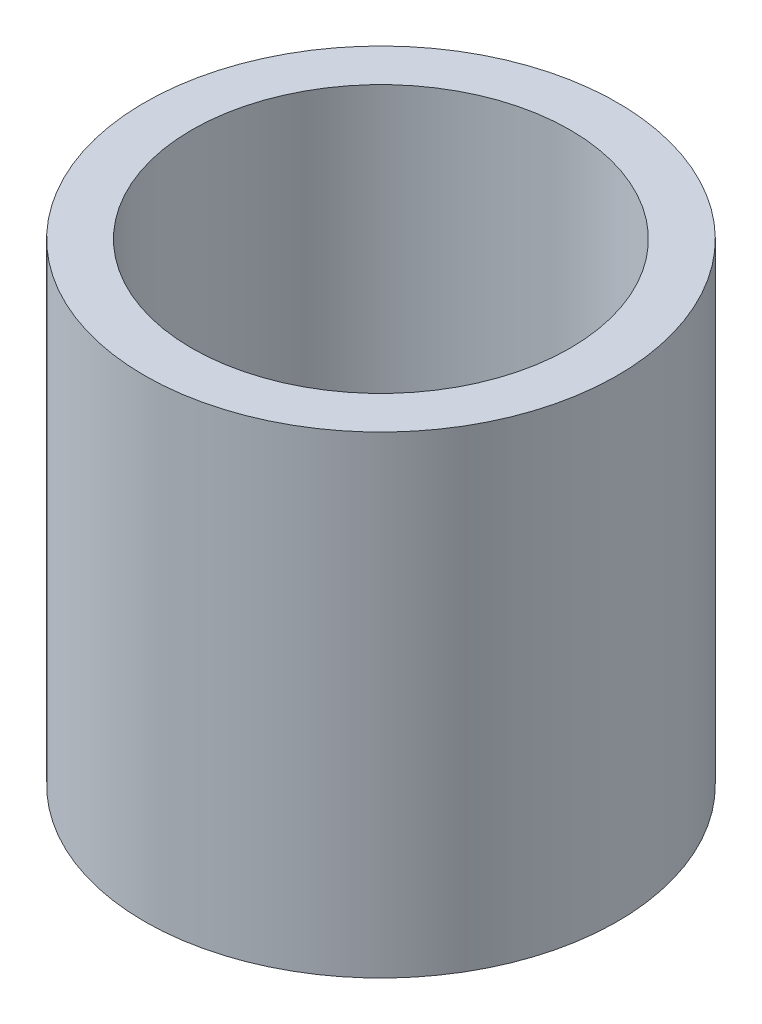
SolidWorks part; units mm, degrees
ref_plane "Front Plane" through (0, 0, 0) normal (0, 0, 1) x (1, 0, 0)
ref_plane "Top Plane" through (0, 0, 0) normal (0, 1, 0) x (1, 0, 0)
ref_plane "Right Plane" through (0, 0, 0) normal (1, 0, 0) x (0, 0, -1)
sketch "Sketch1" plane through (0, 0, 0) normal (0, 1, 0) x (1, 0, 0)
  circle A0 centre (0, 0) radius 4
  circle A1 centre (0, 0) radius 5
  dimension "D1" = 8
  dimension "D2" = 1
extrude "Boss-Extrude1" add sketch "Sketch1" along normal blind 10
